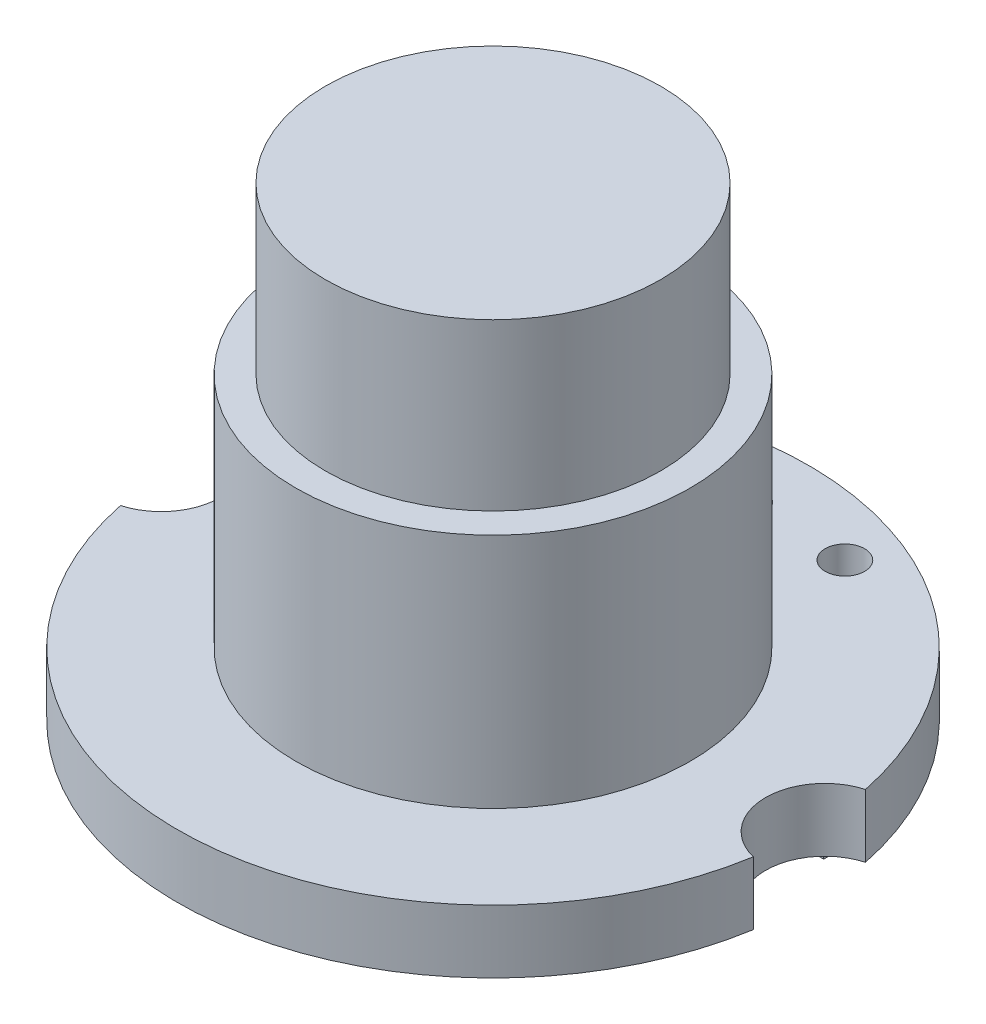
SolidWorks part; units mm, degrees
ref_plane "前视基准面" through (0, 0, 0) normal (0, 0, 1) x (1, 0, 0)
ref_plane "上视基准面" through (0, 0, 0) normal (0, 1, 0) x (1, 0, 0)
ref_plane "右视基准面" through (0, 0, 0) normal (1, 0, 0) x (0, 0, -1)
sketch "草图1" plane through (0, 0, 0) normal (0, 1, 0) x (1, 0, 0)
  line L0 (0, 0) -> (0.0544, -2.772) construction
  line L1 (-3.2831, -0.0645) -> (3.2831, 0.0645) construction
  arc A2 (7.8944, -1.2957) -> (7.8374, 1.6046) centre (8.2484, 0.1619) cw
  arc A3 (-7.8374, -1.6046) -> (-7.8944, 1.2957) centre (-8.2484, -0.1619) ccw
  arc A4 (-7.8374, -1.6046) -> (7.8944, -1.2957) centre (0, 0) ccw
  arc A5 (7.8374, 1.6046) -> (-7.8944, 1.2957) centre (0, 0) ccw
  point P1 (6.7487, 0.1325)
  point P3 (-6.7487, -0.1325)
  point P10 (0, 0)
  dimension "D1" = 13.5
  dimension "D3" = 1.5
  dimension "D4" = 8
extrude "凸台-拉伸1" add sketch "草图1" along normal blind 1.6
sketch "草图2" plane through (0, 1.6, 0) normal (0, 1, 0) x (1, 0, 0)
  circle A0 centre (0, 0) radius 5
  dimension "D1" = 10
extrude "凸台-拉伸2" add sketch "草图2" along normal blind 6
sketch "草图3" plane through (0, 7.6, 0) normal (0, 1, 0) x (1, 0, 0)
  circle A0 centre (0, 0) radius 4.25
  dimension "D1" = 8.5
extrude "凸台-拉伸3" add sketch "草图3" along normal blind 10.2 from surface at -6 starting at face at (0, 1.6, 5)
sketch "草图4" plane through (0, 1.6, 0) normal (0, 1, 0) x (1, 0, 0)
  circle A0 centre (-2.54, 6.3801) radius 0.5
  circle A1 centre (0, 6.3801) radius 0.5
  circle A2 centre (2.54, 6.3801) radius 0.5
  dimension "D1" = 1
  dimension "D2" = 3
extrude "切除-拉伸1" cut sketch "草图4" against normal through all
sketch "草图5" plane through (0, 0, 0) normal (0, -1, 0) x (1, 0, 0)
  line L1 (4.5632, -2.844) -> (5.5395, -2.844)
  line L2 (4.5632, -2.844) -> (4.5632, -4.8816)
  line L3 (4.5632, -4.8816) -> (5.5395, -4.8816)
  line L4 (5.5395, -2.844) -> (5.5395, -4.8816)
extrude "凸台-拉伸4" add sketch "草图5" along normal blind 3.3 from surface at -1.6 starting at face at (-2.54, 1.6, -5.8801)
